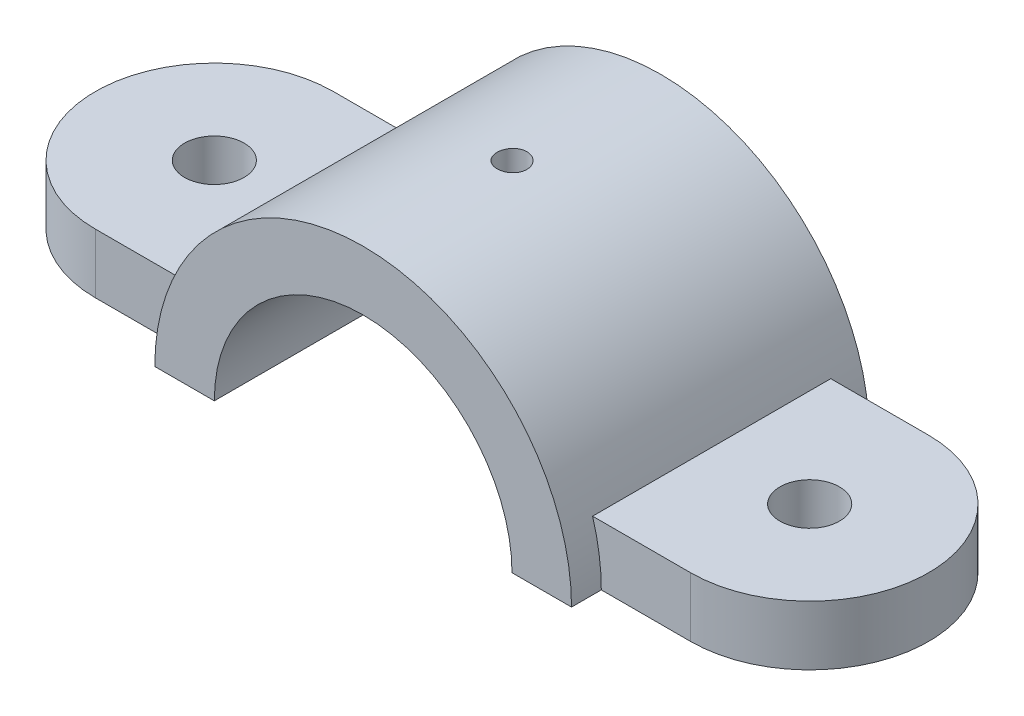
SolidWorks part; units mm, degrees
ref_plane "Front Plane" through (0, 0, 0) normal (0, 0, 1) x (1, 0, 0)
ref_plane "Top Plane" through (0, 0, 0) normal (0, 1, 0) x (1, 0, 0)
ref_plane "Right Plane" through (0, 0, 0) normal (1, 0, 0) x (0, 0, -1)
sketch "Sketch1" plane through (0, 0, 0) normal (0, 1, 0) x (1, 0, 0)
  line L0 (-63.5, 0) -> (63.5, 0) construction
  line L1 (-63.5, 25.4) -> (63.5, 25.4)
  line L2 (-63.5, -25.4) -> (63.5, -25.4)
  arc A0 (-63.5, 25.4) -> (-63.5, -25.4) centre (-63.5, 0) ccw
  arc A1 (63.5, -25.4) -> (63.5, 25.4) centre (63.5, 0) ccw
  circle A2 centre (-63.5, 0) radius 6.35
  circle A3 centre (63.5, 0) radius 6.35
  point P2 (0, 0)
  dimension "D2" = 12.7
  dimension "D3" = 12.7
  dimension "D4" = 25.4
  dimension "D1" = 127
extrude "Boss-Extrude1" add sketch "Sketch1" along normal blind 12.7
sketch "Sketch2" plane through (0, 0, 0) normal (0, 0, 1) x (1, 0, 0)
  line L0 (-63.5, 0) -> (63.5, 0) construction
  line L1 (-44.45, 0) -> (44.45, 0)
  arc A0 (44.45, 0) -> (-44.45, 0) centre (0, 0) ccw
  dimension "D1" = 44.45
extrude "Boss-Extrude2" add sketch "Sketch2" along normal mid plane 63.5
sketch "Sketch3" plane through (0, 0, 0) normal (0, 0, 1) x (1, 0, 0)
  circle A0 centre (0, 0) radius 31.75
  dimension "D1" = 63.5
extrude "Cut-Extrude1" cut sketch "Sketch3" against normal mid plane 63.5
sketch "Sketch4" plane through (0, 0, 0) normal (0, 1, 0) x (1, 0, 0)
  circle A0 centre (0, 0) radius 3.175
  dimension "D1" = 6.35
extrude "Cut-Extrude2" cut sketch "Sketch4" along normal blind 63.5
